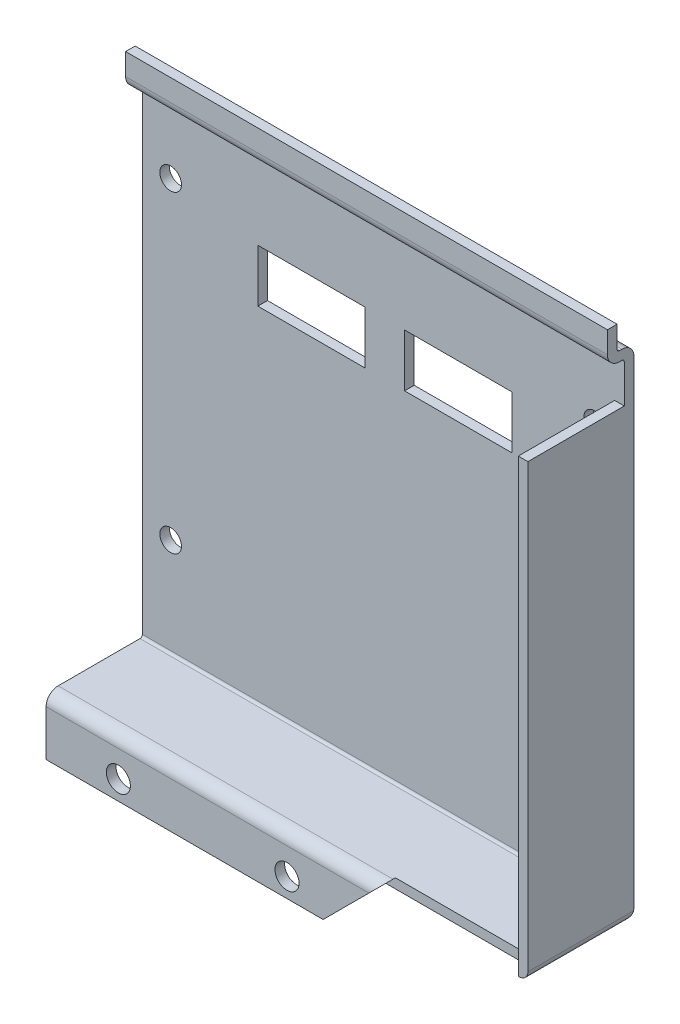
SolidWorks part; units mm, degrees
ref_plane "Front Plane" through (0, 0, 0) normal (0, 0, 1) x (1, 0, 0)
ref_plane "Top Plane" through (0, 0, 0) normal (0, 1, 0) x (1, 0, 0)
ref_plane "Right Plane" through (0, 0, 0) normal (1, 0, 0) x (0, 0, -1)
sketch "Sketch1" plane through (0, 0, 0) normal (1, 0, 0) x (0, 0, -1)
  line L0 (0, -2.5) -> (0, -12)
  line L1 (2.5, 0) -> (19.5, 0)
  line L2 (20, 0.5) -> (20, 99.5)
  line L3 (19.5, 100) -> (19, 100)
  line L4 (16.5, 102.5) -> (16.5, 107)
  line L5 (16.5, 107) -> (18.5, 107)
  line L6 (18.5, 107) -> (18.5, 102.5)
  line L7 (19, 102) -> (19.5, 102)
  line L8 (22, 99.5) -> (22, 0.5)
  line L9 (19.5, -2) -> (2.5, -2)
  line L10 (2, -2.5) -> (2, -12)
  line L11 (2, -12) -> (0, -12)
  arc A0 (2.5, -2) -> (2, -2.5) centre (2.5, -2.5) ccw
  arc A1 (19.5, 0) -> (20, 0.5) centre (19.5, 0.5) ccw
  arc A2 (20, 99.5) -> (19.5, 100) centre (19.5, 99.5) ccw
  arc A3 (18.5, 102.5) -> (19, 102) centre (19, 102.5) ccw
  arc A4 (16.5, 102.5) -> (19, 100) centre (19, 102.5) ccw
  arc A5 (22, 99.5) -> (19.5, 102) centre (19.5, 99.5) ccw
  arc A6 (19.5, -2) -> (22, 0.5) centre (19.5, 0.5) ccw
  arc A7 (2.5, 0) -> (0, -2.5) centre (2.5, -2.5) ccw
  point P17 (20, 0)
  point P20 (20, 100)
  dimension "D7" = 0.5
  dimension "D1" = 3.5
  dimension "D2" = 20
  dimension "D3" = 10
  dimension "D4" = 5
  dimension "D5" = 100
  dimension "D6" = 2
extrude "Boss-Extrude1" add sketch "Sketch1" along normal blind 100
sketch "Sketch2" plane through (0, 0, -20) normal (0, 0, 1) x (1, 0, 0)
  line L0 (100, -12) -> (0, -12) construction
  line L1 (100, 0.5) -> (97.5, 0.5)
  line L2 (100, 0.5) -> (100, -12)
  line L3 (100, -12) -> (97.5, -12)
  line L4 (97.5, 0.5) -> (97.5, -12)
  dimension "D1" = 2.5
extrude "Cut-Extrude1" cut sketch "Sketch2" along normal through all
sketch "Sketch3" plane through (0, 0, -20) normal (0, 0, 1) x (1, 0, 0)
  line L1 (100, -1.9495) -> (98, -1.9495)
  line L2 (100, -1.9495) -> (100, 91.5505)
  line L3 (100, 91.5505) -> (98, 91.5505)
  line L4 (98, -1.9495) -> (98, 91.5505)
  dimension "D1" = 2
  dimension "D2" = 93.5
extrude "Boss-Extrude2" add sketch "Sketch3" along normal blind 20
sketch "Sketch4" plane through (0, 0, 0) normal (0, 0, 1) x (1, 0, 0)
  line L0 (97.5, 0) -> (69.5, 0)
  line L1 (97.5, -2.5) -> (97.5, -12) construction
  line L2 (69.5, 0) -> (57.5, -12)
  line L3 (97.5, -12) -> (0, -12) construction
  line L4 (57.5, -12) -> (97.5, -12)
  line L5 (97.5, -12) -> (97.5, 0)
  line L6 (0, -2.5) -> (0, -12) construction
  line L7 (97.5, 0) -> (0, 0) construction
  circle A0 centre (15, -8) radius 2.5
  circle A1 centre (50, -8) radius 2.5
  dimension "D4" = 5
  dimension "D1" = 15
  dimension "D2" = 4
  dimension "D3" = 35
  dimension "D5" = 7.5
  dimension "D6" = 45
extrude "Cut-Extrude3" cut sketch "Sketch4" against normal blind 3
sketch "Sketch5" plane through (0, 0, -20) normal (0, 0, 1) x (1, 0, 0)
  line L0 (75.65, 81.42) -> (75.65, 72.47) construction
  line L1 (23.95, 82.42) -> (46.2, 82.42)
  line L2 (23.95, 82.42) -> (23.95, 71.47)
  line L3 (23.95, 71.47) -> (46.2, 71.47)
  line L4 (46.2, 82.42) -> (46.2, 71.47)
  line L5 (54.4, 82.42) -> (76.65, 82.42)
  line L6 (54.4, 82.42) -> (54.4, 71.47)
  line L7 (54.4, 71.47) -> (76.65, 71.47)
  line L8 (76.65, 82.42) -> (76.65, 71.47)
  line L9 (45.2, 81.42) -> (45.2, 72.47) construction
  line L10 (55.4, 72.47) -> (55.4, 81.42) construction
  line L11 (24.95, 72.47) -> (24.95, 81.42) construction
  line L12 (45.2, 72.47) -> (24.95, 72.47) construction
  line L13 (24.95, 81.42) -> (45.2, 81.42) construction
  circle A0 centre (5.85, 85.37) radius 2.25
  circle A1 centre (5.85, 20.37) radius 2.25
  circle A2 centre (93.85, 20.37) radius 2.25
  circle A3 centre (93.85, 85.37) radius 2.25
  dimension "D1" = 4.5
  dimension "D2" = 1
  dimension "D3" = 1
  dimension "D4" = 1
  dimension "D5" = 1
  dimension "D6" = 1
  dimension "D7" = 1
extrude "Cut-Extrude4" cut sketch "Sketch5" against normal blind 5
fillet "Fillet1" radius 1.8 1 edges at (100, -1.9495, -10)
